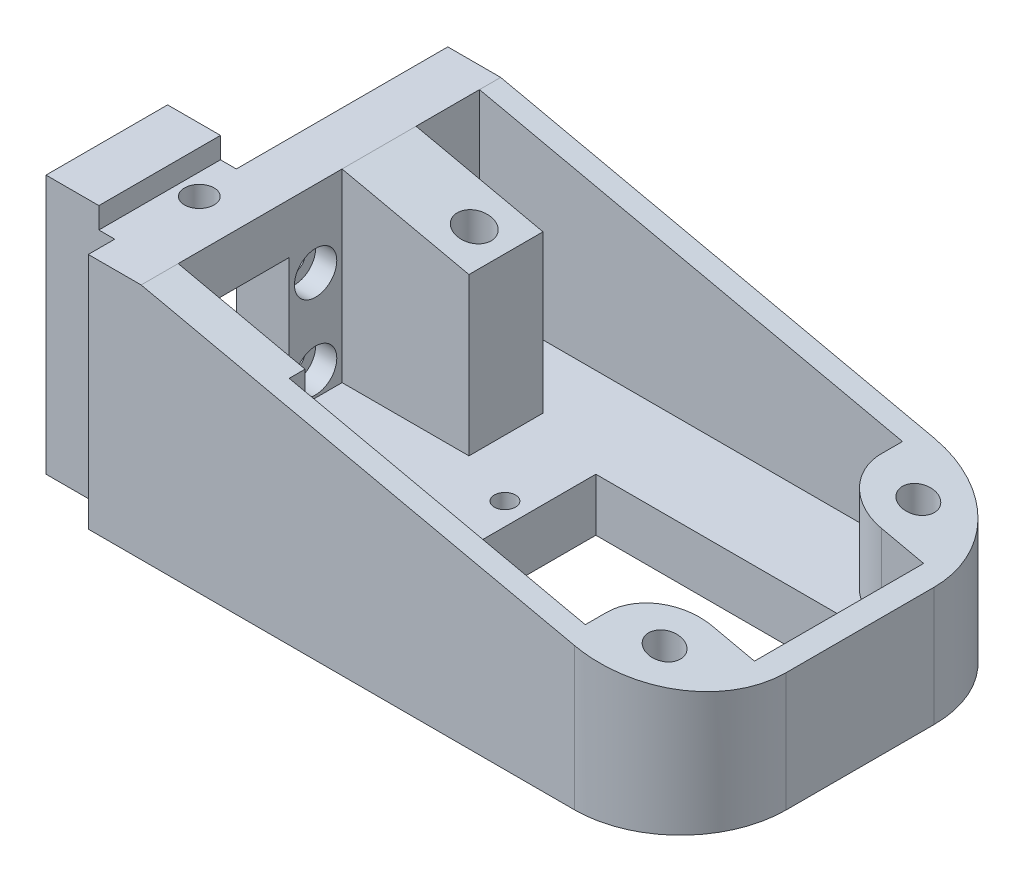
SolidWorks part; units mm, degrees
ref_plane "Front Plane" through (0, 0, 0) normal (0, 0, 1) x (1, 0, 0)
ref_plane "Top Plane" through (0, 0, 0) normal (0, 1, 0) x (1, 0, 0)
ref_plane "Right Plane" through (0, 0, 0) normal (1, 0, 0) x (0, 0, -1)
sketch "Sketch2" plane through (0, 0, 0) normal (0, 1, 0) x (1, 0, 0)
  line L0 (0, 14) -> (0, 0) construction
  line L1 (0, 0) -> (46, 0)
  line L2 (0, 14) -> (0, 34)
  line L3 (0, 34) -> (46, 34)
  line L4 (56, 10) -> (56, 24)
  line L5 (0, 0) -> (-6.5, 0)
  line L7 (0, 14) -> (-6.5, 14)
  line L8 (-6.5, 0) -> (-6.5, 14)
  arc A0 (46, 0) -> (56, 10) centre (46, 10) ccw
  arc A1 (46, 34) -> (56, 24) centre (46, 24) cw
  dimension "D5" = 10
  dimension "D1" = 34
  dimension "D2" = 20
  dimension "D3" = 6.5
  dimension "D4" = 56
extrude "Boss-Extrude1" add sketch "Sketch2" along normal blind 22.5
sketch "Sketch3" plane through (0, 22.5, 0) normal (0, 1, 0) x (1, 0, 0)
  line L0 (46, 34) -> (0, 34) construction
  line L1 (5, 32) -> (45, 32)
  line L2 (5, 32) -> (5, 2)
  line L3 (5, 2) -> (45, 2)
  line L4 (45, 32) -> (45, 30)
  line L5 (50, 25) -> (54, 25)
  line L7 (50, 9) -> (54, 9)
  line L8 (54, 25) -> (54, 9)
  line L9 (-6.5, 0) -> (46, 0) construction
  line L10 (56, 10) -> (56, 24) construction
  line L11 (45, 4) -> (45, 2)
  line L12 (45, 25) -> (45, 9) construction
  line L13 (45, 9) -> (45, 4) construction
  line L14 (0, 34) -> (0, 14) construction
  line L15 (54, 17) -> (56, 17) construction
  line L17 (5, 3.5) -> (17, 3.5)
  line L18 (5, 3.5) -> (5, 2)
  line L19 (5, 2) -> (17, 2)
  line L20 (17, 3.5) -> (17, 2)
  arc A0 (45, 4) -> (50, 9) centre (50, 4) cw
  arc A1 (50, 25) -> (45, 30) centre (50, 30) cw
  dimension "D6" = 5
  dimension "D7" = 12
  dimension "D10" = 1.5
  dimension "D1" = 2
  dimension "D2" = 2
  dimension "D3" = 7
  dimension "D4" = 7
  dimension "D5" = 2
  dimension "D8" = 5
  dimension "D9" = 40
extrude "Cut-Extrude1" cut sketch "Sketch3" against normal blind 17.5 contours L5 A1 L4 L1 L2 L17 L20 L3 L11 A0 L7 L8
sketch "Sketch4" plane through (5, 0, 0) normal (1, 0, 0) x (0, 0, -1)
  line L0 (34, 22.5) -> (34, 0) construction
  line L1 (16.5, 7.25) -> (28.5, 7.25) construction
  line L2 (16.5, 7.25) -> (16.5, 15.25) construction
  line L3 (16.5, 15.25) -> (28.5, 15.25) construction
  line L4 (28.5, 7.25) -> (28.5, 15.25) construction
  line L5 (16.5, 7.25) -> (28.5, 15.25) construction
  line L6 (16.5, 15.25) -> (28.5, 7.25) construction
  line L7 (34, 0) -> (14, 0) construction
  circle A0 centre (28.5, 15.25) radius 1
  circle A1 centre (28.5, 7.25) radius 1
  circle A2 centre (16.5, 7.25) radius 1
  circle A3 centre (16.5, 15.25) radius 1
  point P0 (22.5, 11.25)
  dimension "D6" = 2
  dimension "D7" = 2
  dimension "D8" = 2
  dimension "D9" = 2
  dimension "D1" = 12
  dimension "D2" = 12
  dimension "D3" = 5.5
  dimension "D4" = 7.25
  dimension "D5" = 8
extrude "Cut-Extrude2" cut sketch "Sketch4" against normal through all and the other way blind 15
sketch "Sketch5" plane through (-6.5, 0, 0) normal (-1, 0, 0) x (0, 0, 1)
  line L0 (-14, 0) -> (0, 0) construction
  line L1 (-3.5, 17.75) -> (-14, 17.75)
  line L2 (-3.5, 17.75) -> (-3.5, 5.25)
  line L3 (-3.5, 5.25) -> (-14, 5.25)
  line L4 (-14, 17.75) -> (-14, 5.25)
  line L5 (-14, 22.5) -> (-14, 0) construction
  dimension "D2" = 10.5
  dimension "D3" = 5.25
  dimension "D4" = 12.5
extrude "Cut-Extrude3" cut sketch "Sketch5" against normal blind 20
sketch "Sketch6" plane through (0, 22.5, 0) normal (0, 1, 0) x (1, 0, 0)
  line L0 (-6.5, 14) -> (-6.5, 0) construction
  line L1 (-6.5, 0) -> (46, 0) construction
  circle A0 centre (0.5, 10) radius 1.4
  point P4 (-6.5, 7)
  dimension "D1" = 2.8
  dimension "D2" = 7
  dimension "D3" = 10
extrude "Cut-Extrude4" cut sketch "Sketch6" against normal blind 10
sketch "Sketch8" plane through (0, 5, 0) normal (0, 1, 0) x (1, 0, 0)
  line L0 (48.5, 17) -> (54, 17) construction
  line L1 (24.5, 23.5) -> (48.5, 23.5)
  line L2 (24.5, 23.5) -> (24.5, 10.5)
  line L3 (24.5, 10.5) -> (48.5, 10.5)
  line L4 (48.5, 23.5) -> (48.5, 10.5)
  line L5 (54, 9) -> (54, 25) construction
  line L6 (24.5, 17) -> (21.4, 17) construction
  circle A0 centre (50.6, 17) radius 1
  circle A1 centre (22.4, 17) radius 1
  dimension "D4" = 2
  dimension "D5" = 2
  dimension "D7" = 2.1
  dimension "D1" = 13
  dimension "D2" = 24
  dimension "D3" = 5.5
  dimension "D6" = 2.1
extrude "Cut-Extrude6" cut sketch "Sketch8" against normal through all
sketch "Sketch9" plane through (0, 22.5, 0) normal (0, 1, 0) x (1, 0, 0)
  line L0 (49.5, 29) -> (49.5, 5) construction
  line L1 (49.5, 17) -> (54, 17) construction
  line L2 (54, 9) -> (54, 25) construction
  circle A0 centre (49.5, 29) radius 1.5
  circle A1 centre (49.5, 5) radius 1.5
  dimension "D2" = 3
  dimension "D3" = 3
  dimension "D1" = 24
  dimension "D4" = 4.5
extrude "Cut-Extrude7" cut sketch "Sketch9" against normal through all
sketch "Sketch10" plane through (0, 0, 0) normal (0, -1, 0) x (1, 0, 0)
  circle A0 centre (49.5, -5) radius 3
  circle A1 centre (49.5, -29) radius 3
  dimension "D1" = 6
  dimension "D2" = 6
extrude "Cut-Extrude8" cut sketch "Sketch10" against normal blind 5
ref_plane "Plane1" through (0, 0, -22.5) normal (0, 0, 1) x (1, 0, 0)
sketch "Sketch14" plane through (0, 0, -22.5) normal (0, 0, 1) x (1, 0, 0)
  line L0 (5, 22.5) -> (5, 5)
  line L2 (5, 5) -> (5, 22.5) construction
  line L3 (5, 5) -> (17, 5)
  line L5 (-6.5, 0) -> (46, 0) construction
  line L6 (5, 22.5) -> (17, 22.5)
  line L7 (5, 22.5) -> (45, 22.5) construction
  line L8 (17, 22.5) -> (17, 5)
  dimension "D1" = 12
  dimension "D2" = 5
extrude "Boss-Extrude3" add sketch "Sketch14" along normal mid plane 7
sketch "Sketch11" plane through (0, 0, 0) normal (0, -1, 0) x (1, 0, 0)
  line L0 (8, -8) -> (8, -26) construction
  line L1 (8, -17) -> (56, -17) construction
  line L3 (56, -10) -> (56, -24) construction
  line L4 (-6.5, 0) -> (46, 0) construction
  line L5 (46, -34) -> (0, -34) construction
  circle A0 centre (8, -8) radius 1.5
  circle A1 centre (8, -26) radius 1.5
  dimension "D3" = 3
  dimension "D4" = 3
  dimension "D1" = 18
  dimension "D2" = 48
extrude "Cut-Extrude9" cut sketch "Sketch11" against normal blind 10
sketch "Sketch16" plane through (5, 0, 0) normal (1, 0, 0) x (0, 0, -1)
  circle A0 centre (28.5, 15.25) radius 2
  circle A1 centre (28.5, 7.25) radius 2
  circle A2 centre (16.5, 7.25) radius 2
  circle A3 centre (16.5, 15.25) radius 2
  dimension "D1" = 4
  dimension "D2" = 4
  dimension "D3" = 4
  dimension "D4" = 4
extrude "Cut-Extrude11" cut sketch "Sketch16" against normal blind 2
sketch "Sketch18" plane through (0, 22.5, 0) normal (0, 1, 0) x (1, 0, 0)
  line L1 (-6.5, 0) -> (0, 0)
  line L2 (-6.5, 0) -> (-6.5, 2.5)
  line L3 (-6.5, 2.5) -> (0, 2.5)
  line L4 (0, 0) -> (0, 2.5)
  dimension "D1" = 6.5
  dimension "D2" = 2.5
extrude "Cut-Extrude12" cut sketch "Sketch18" against normal through all
sketch "Sketch21" plane through (0, 0, 0) normal (0, 0, 1) x (1, 0, 0)
  line L0 (5, 22.5) -> (56, 11.25)
  line L1 (56, 22.5) -> (56, 0) construction
  line L2 (56, 11.25) -> (56, 22.5)
  line L3 (56, 22.5) -> (5, 22.5)
  dimension "D1" = 11.25
extrude "Cut-Extrude14" cut sketch "Sketch21" against normal through all
sketch "Sketch22" plane through (0, 0, 0) normal (0, -1, 0) x (1, 0, 0)
  line L0 (14, -22.5) -> (17, -22.5) construction
  line L1 (17, -19) -> (17, -26) construction
  circle A0 centre (14, -22.5) radius 1.6
  dimension "D1" = 3.2
  dimension "D2" = 3
extrude "Cut-Extrude15" cut sketch "Sketch22" against normal through all
sketch "Sketch23" plane through (0, 0, 0) normal (0, -1, 0) x (1, 0, 0)
  circle A0 centre (14, -22.5) radius 3
  dimension "D1" = 6
extrude "Cut-Extrude18" cut sketch "Sketch23" against normal blind 3
sketch "Sketch25" plane through (0, 22.5, 0) normal (0, 1, 0) x (1, 0, 0)
  line L0 (0, 14) -> (-6.5, 14) construction
  line L1 (-6.5, 14) -> (-1.5, 14)
  line L2 (-6.5, 14) -> (-6.5, 2.5)
  line L3 (-6.5, 2.5) -> (-1.5, 2.5)
  line L4 (-1.5, 14) -> (-1.5, 2.5)
  line L5 (-6.5, 14) -> (-6.5, 2.5) construction
  dimension "D1" = 5
extrude "Boss-Extrude4" add sketch "Sketch25" along normal blind 2
